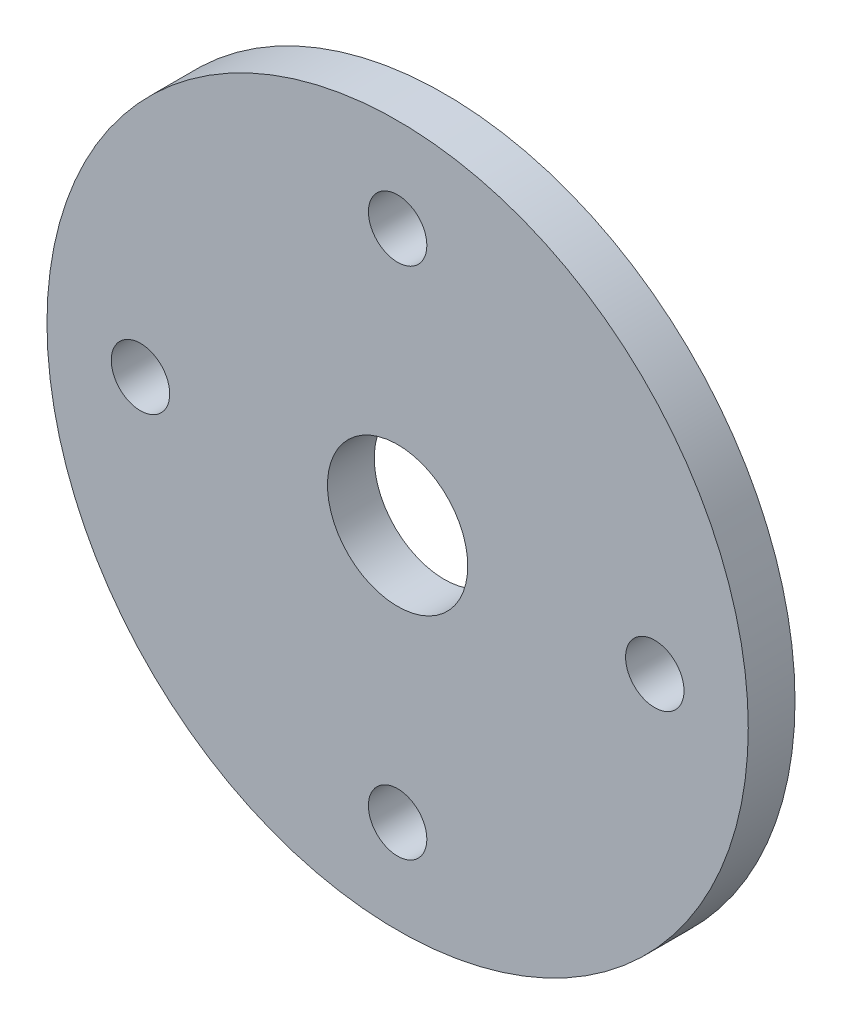
SolidWorks part; units mm, degrees
material "1.0038 (S235JRG2)"
ref_plane "Plan de face" through (0, 0, 0) normal (0, 0, 1) x (1, 0, 0)
ref_plane "Plan de dessus" through (0, 0, 0) normal (0, 1, 0) x (1, 0, 0)
ref_plane "Plan de droite" through (0, 0, 0) normal (1, 0, 0) x (0, 0, -1)
sketch "Esquisse1" plane through (0, 0, 0) normal (0, 0, 1) x (1, 0, 0)
  line L0 (0, 0) -> (-55, 0) construction
  line L1 (-55, 0) -> (0, 55) construction
  line L2 (0, -55) -> (0, 0) construction
  line L3 (0, 0) -> (55, 0) construction
  line L4 (0, 55) -> (55, 0) construction
  line L5 (0, 55) -> (0, 0) construction
  line L6 (55, 0) -> (0, -55) construction
  line L7 (0, -55) -> (-55, 0) construction
  circle A0 centre (0, 0) radius 75
  circle A1 centre (0, 0) radius 55 construction
  circle A2 centre (0, 0) radius 15
  circle A3 centre (0, 55) radius 6.25
  circle A4 centre (-55, 0) radius 6.25
  circle A5 centre (0, -55) radius 6.25
  circle A6 centre (55, 0) radius 6.25
  dimension "D1" = 30
  dimension "D2" = 110
  dimension "D3" = 150
  dimension "D4" = 12.5
extrude "Boss.-Extru.1" add sketch "Esquisse1" along normal mid plane 10
